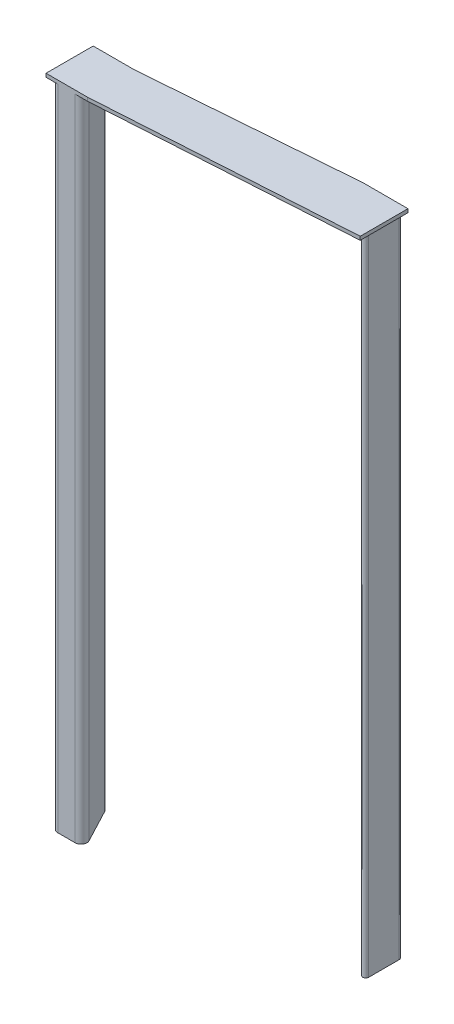
SolidWorks part; units mm, degrees
ref_plane "Front Plane" through (0, 0, 0) normal (0, 0, 1) x (1, 0, 0)
ref_plane "Top Plane" through (0, 0, 0) normal (0, 1, 0) x (1, 0, 0)
ref_plane "Right Plane" through (0, 0, 0) normal (1, 0, 0) x (0, 0, -1)
sketch "Sketch1" plane through (0, 0, 0) normal (0, 1, 0) x (1, 0, 0)
  line L0 (0, 0) -> (0, 21.2)
  line L1 (0, 21.2) -> (11.2, 0)
  line L2 (11.2, 0) -> (0, 0)
  dimension "D1" = 11.2
  dimension "D2" = 21.2
extrude "Boss-Extrude1" add sketch "Sketch1" along normal blind 220
fillet "Fillet1" radius 2 3 edges at (11.2, 110, 0) (0, 110, 0) (0, 110, -21.2)
sketch "Sketch5" plane through (0, 0, 0) normal (0, -1, 0) x (1, 0, 0)
  line L0 (86, -21.6) -> (97.2, -21.6)
  line L1 (97.2, -21.6) -> (97.2, -7.4)
  line L2 (97.2, -7.4) -> (86, -21.6)
  line L4 (2, 0) -> (7.8814, 0) construction
  line L5 (0, -13.1327) -> (0, -2) construction
  dimension "D1" = 11.2
  dimension "D2" = 14.2
  dimension "D3" = 97.2
  dimension "D4" = 21.6
extrude "Boss-Extrude5" add sketch "Sketch5" against normal up to surface (220 mm away) separate body up to face at (3.8915, 220, -5.4491)
sketch "Sketch3" plane through (0, 0, 0) normal (0, -1, 0) x (1, 0, 0)
  line L0 (2, 0) -> (7.8814, 0) construction
  line L1 (97.2, -21.6) -> (97.2, -7.4) construction
  line L2 (0, -13.1327) -> (0, -2) construction
  line L3 (86, -21.6) -> (97.2, -21.6) construction
  circle A0 centre (4, -4) radius 2
  circle A1 centre (93.6, -18) radius 2
  dimension "D1" = 4
  dimension "D2" = 4
  dimension "D3" = 4
  dimension "D4" = 3.6
  dimension "D5" = 3.6
  dimension "D6" = 4
extrude "Cut-Extrude1" cut sketch "Sketch3" against normal blind 5
sketch "Sketch4" plane through (0, 0, 0) normal (0, -1, 0) x (1, 0, 0)
  line L1 (2, -7.2) -> (4.4, -7.2)
  line L2 (2, -7.2) -> (2, -9.6)
  line L3 (2, -9.6) -> (4.4, -9.6)
  line L4 (4.4, -7.2) -> (4.4, -9.6)
  circle A0 centre (4, -4) radius 2 construction
  dimension "D1" = 3.2
  dimension "D2" = 2
  dimension "D3" = 2.4
  dimension "D4" = 2.4
extrude "Cut-Extrude2" cut sketch "Sketch4" against normal blind 2
sketch "Sketch6" plane through (0, 220, 0) normal (0, 1, 0) x (1, 0, 0)
  line L1 (99.2, 21.6) -> (84, 21.6)
  line L2 (99.2, 21.6) -> (99.2, 5.4)
  line L6 (12, 16) -> (84, 21.6)
  line L7 (99.2, 5.4) -> (12, 0)
  line L9 (97.2, 7.4) -> (97.2, 21.6) construction
  line L10 (0, 13.1327) -> (0, 2) construction
  line L11 (12, 16) -> (-2, 16)
  line L13 (12, 0) -> (-2, 0)
  line L14 (-2, 16) -> (-2, 0)
  dimension "D1" = 2
  dimension "D2" = 2
extrude "Boss-Extrude4" add sketch "Sketch6" along normal blind 1.2
fillet "Fillet2" radius 1 3 edges at (97.2, 110, -7.4) (97.2, 110, -21.6) (86, 110, -21.6)
